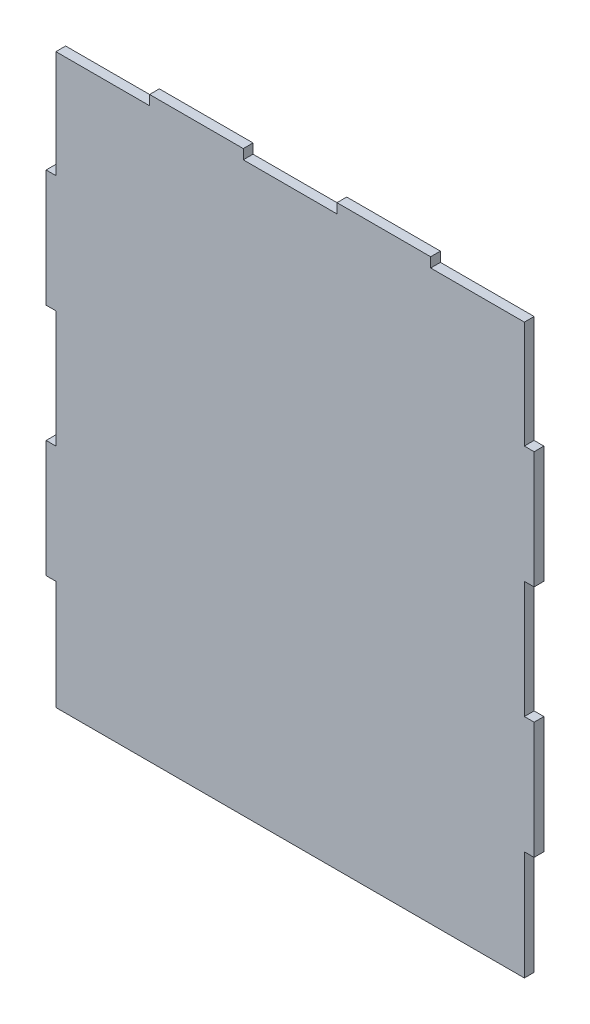
SolidWorks part; units mm, degrees
material "Contreplaqué pin"
ref_plane "Plan de face" through (0, 0, 0) normal (0, 0, 1) x (1, 0, 0)
ref_plane "Plan de dessus" through (0, 0, 0) normal (0, 1, 0) x (1, 0, 0)
ref_plane "Plan de droite" through (0, 0, 0) normal (1, 0, 0) x (0, 0, -1)
sketch "Esquisse1" plane through (0, 0, 0) normal (0, 0, 1) x (1, 0, 0)
  line L0 (5, 291) -> (5, 236)
  line L1 (5, 0) -> (245, 0)
  line L3 (53, 296) -> (101, 296)
  line L4 (250, 56) -> (250, 116)
  line L5 (5, 236) -> (0, 236)
  line L6 (0, 176) -> (5, 176)
  line L7 (5, 176) -> (5, 116)
  line L8 (5, 116) -> (0, 116)
  line L9 (0, 56) -> (5, 56)
  line L12 (0, 176) -> (0, 236)
  line L13 (0, 56) -> (0, 116)
  line L14 (5, 56) -> (5, 0)
  line L15 (245, 291) -> (245, 236)
  line L16 (245, 236) -> (250, 236)
  line L17 (250, 176) -> (245, 176)
  line L18 (245, 176) -> (245, 116)
  line L19 (245, 116) -> (250, 116)
  line L20 (250, 56) -> (245, 56)
  line L21 (245, 56) -> (245, 0)
  line L22 (250, 176) -> (250, 236)
  line L23 (5, 291) -> (53, 291)
  line L24 (53, 291) -> (53, 296)
  line L25 (101, 296) -> (101, 291)
  line L26 (101, 291) -> (149, 291)
  line L27 (149, 291) -> (149, 296)
  line L28 (197, 296) -> (197, 291)
  line L29 (197, 291) -> (245, 291)
  line L30 (149, 296) -> (197, 296)
  point P1 (245, 263.5)
  dimension "D1" = 296
  dimension "D2" = 250
  dimension "D3" = 5
  dimension "D4" = 5
  dimension "D5" = 55
  dimension "D6" = 5
  dimension "D7" = 60
extrude "Boss.-Extru.1" add sketch "Esquisse1" along normal blind 5
